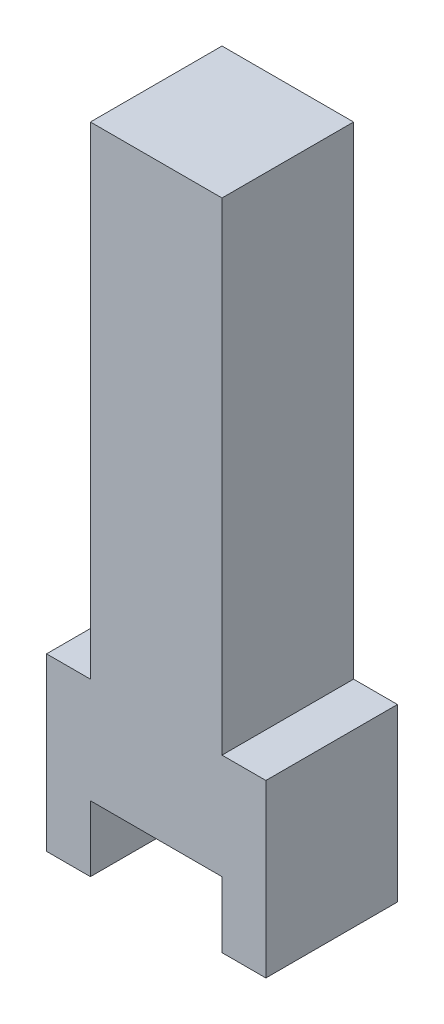
SolidWorks part; units mm, degrees
ref_plane "Front Plane" through (0, 0, 0) normal (0, 0, 1) x (1, 0, 0)
ref_plane "Top Plane" through (0, 0, 0) normal (0, 1, 0) x (1, 0, 0)
ref_plane "Right Plane" through (0, 0, 0) normal (1, 0, 0) x (0, 0, -1)
sketch "Sketch2" plane through (0, 0, 0) normal (0, 0, 1) x (1, 0, 0)
  line L0 (4, -3.9) -> (5, -3.9)
  line L1 (0, 0) -> (1, 0)
  line L2 (0, 0) -> (0, -3.9)
  line L3 (0, -3.9) -> (1, -3.9)
  line L4 (5, 0) -> (5, -3.9)
  line L5 (1, 11) -> (4, 11)
  line L6 (1, 11) -> (1, 0)
  line L7 (1, -2.4) -> (4, -2.4)
  line L8 (4, 11) -> (4, 0)
  line L9 (1, -2.4) -> (1, -3.9)
  line L10 (4, 0) -> (5, 0)
  line L11 (4, -2.4) -> (4, -3.9)
  dimension "D1" = 1.5
  dimension "D2" = 3
  dimension "D3" = 3
  dimension "D4" = 5
  dimension "D5" = 1
  dimension "D6" = 2.4
  dimension "D7" = 1
  dimension "D8" = 11
extrude "Boss-Extrude1" add sketch "Sketch2" along normal blind 3
